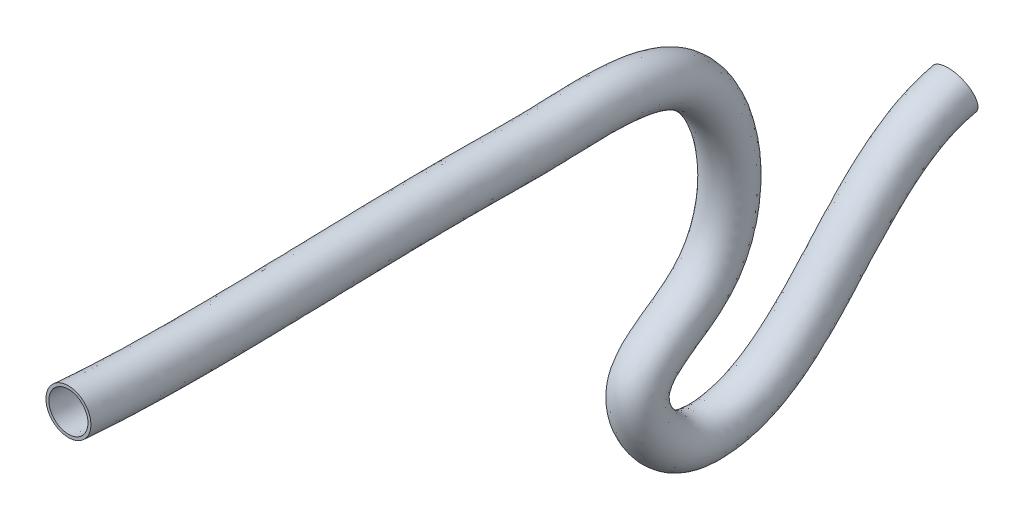
SolidWorks part; units mm, degrees
ref_plane "Front Plane" through (0, 0, 0) normal (0, 0, 1) x (1, 0, 0)
ref_plane "Top Plane" through (0, 0, 0) normal (0, 1, 0) x (1, 0, 0)
ref_plane "Right Plane" through (0, 0, 0) normal (1, 0, 0) x (0, 0, -1)
sketch "Sketch1" plane through (0, 0, 0) normal (0, 0, 1) x (1, 0, 0)
  circle A0 centre (0, 0) radius 1
  circle A1 centre (0, 0) radius 1.15
  dimension "D1" = 2
  dimension "D2" = 2.3
sketch "Sketch5" plane through (0, 0, 0) normal (1, 0, 0) x (0, 0, -1)
  line L0 (0, 1) -> (0, -1) construction
  spline S0 degree 3 poles (0, 0) (6.0828, -0.5499) (15.1812, 0.1421) (25.4465, -0.0871) (33.4195, 0.7283) (35.1139, -10.3449) (27.913, -12.7969) (30.3847, -17.1743) (37.9187, -17.4254) (40.339, -9.4348) (45.3675, -8.3631) knots 0 0 0 0 0.308652 0.366114 0.476792 0.616298 0.684527 0.738823 0.776748 1 1 1 1
  dimension "D1" = 68.261
  dimension "D2" = 45.3675
  dimension "D3" = 8.3631
sweep "Sweep4" add profiles "Sketch1" path "Sketch5"
